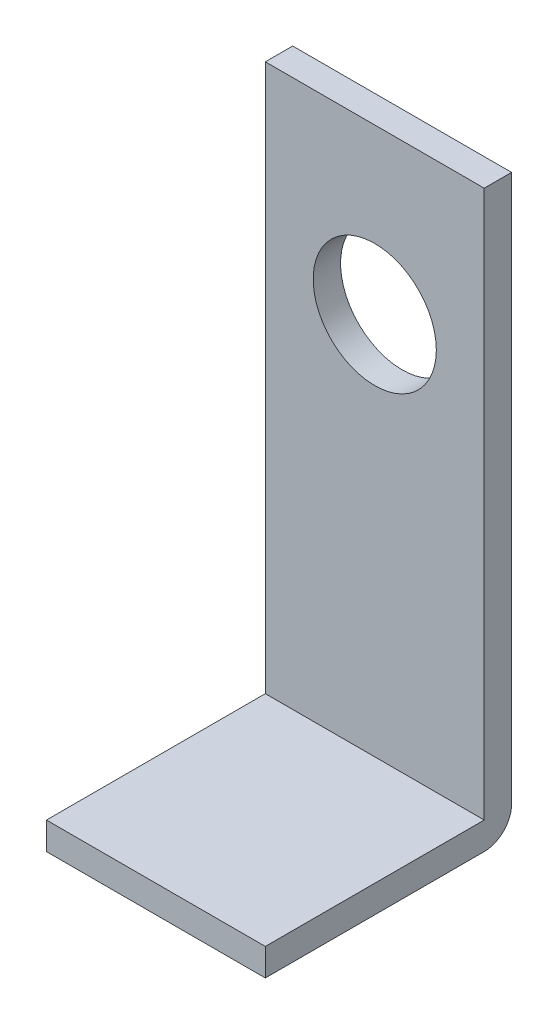
SolidWorks part; units mm, degrees
ref_plane "Front Plane" through (0, 0, 0) normal (0, 0, 1) x (1, 0, 0)
ref_plane "Top Plane" through (0, 0, 0) normal (0, 1, 0) x (1, 0, 0)
ref_plane "Right Plane" through (0, 0, 0) normal (1, 0, 0) x (0, 0, -1)
sketch "Sketch1" plane through (0, 0, 0) normal (0, 0, 1) x (1, 0, 0)
  line L1 (-12.7, -31.75) -> (12.7, -31.75)
  line L2 (-12.7, -31.75) -> (-12.7, 31.75)
  line L3 (-12.7, 31.75) -> (12.7, 31.75)
  line L4 (12.7, -31.75) -> (12.7, 31.75)
  line L5 (-12.7, -31.75) -> (12.7, 31.75) construction
  line L6 (-12.7, 31.75) -> (12.7, -31.75) construction
  point P0 (0, 0)
  dimension "D1" = 25.4
  dimension "D2" = 63.5
extrude "Boss-Extrude1" add sketch "Sketch1" along normal blind 3.175
sketch "Sketch2" plane through (12.7, 0, 0) normal (1, 0, 0) x (0, 0, -1)
  line L1 (-3.175, -31.75) -> (-28.575, -31.75)
  line L2 (-3.175, -31.75) -> (-3.175, -34.925)
  line L3 (-3.175, -34.925) -> (-28.575, -34.925)
  line L4 (-28.575, -31.75) -> (-28.575, -34.925)
  dimension "D1" = 25.4
  dimension "D2" = 3.175
extrude "Boss-Extrude2" add sketch "Sketch2" against normal blind 25.4 separate body
sketch "Sketch3" plane through (12.7, 0, 0) normal (1, 0, 0) x (0, 0, -1)
  line L0 (0, -31.75) -> (-3.175, -31.75)
  line L1 (-3.175, -31.75) -> (-3.175, -34.925)
  arc A0 (-3.175, -34.925) -> (0, -31.75) centre (-3.175, -31.75) ccw
extrude "Boss-Extrude3" add sketch "Sketch3" against normal blind 25.4
sketch "Sketch4" plane through (0, 0, 3.175) normal (0, 0, 1) x (1, 0, 0)
  line L0 (12.7, 31.75) -> (-12.7, 31.75) construction
  circle A0 centre (0, 12.7) radius 7.1438
  dimension "D1" = 14.2875
  dimension "D2" = 19.05
extrude "Cut-Extrude1" cut sketch "Sketch4" against normal through all
